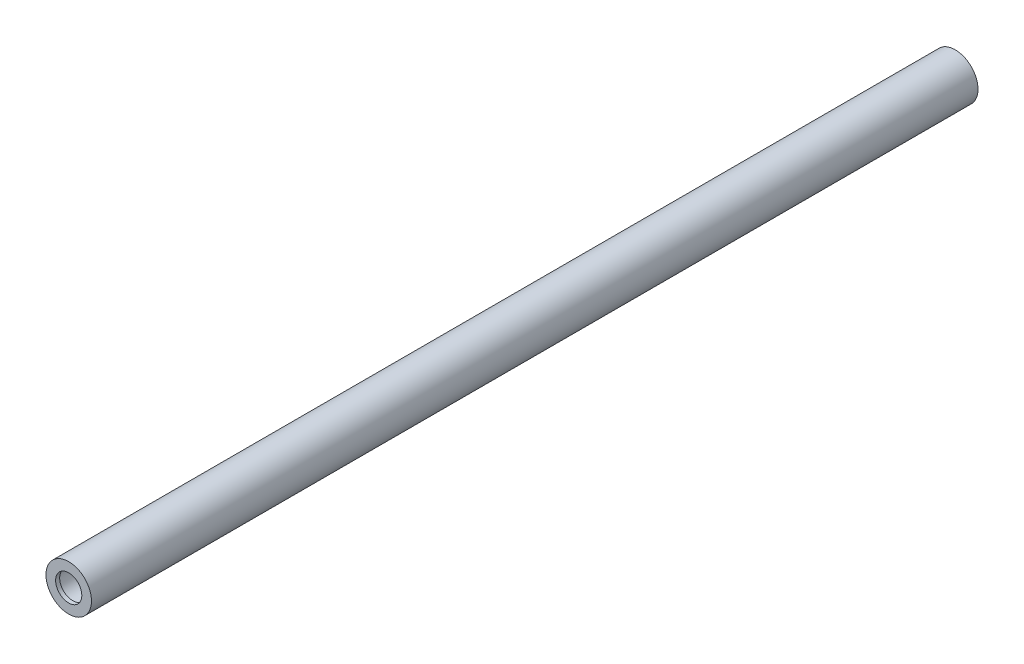
SolidWorks part; units mm, degrees
ref_plane "Front Plane" through (0, 0, 0) normal (0, 0, 1) x (1, 0, 0)
ref_plane "Top Plane" through (0, 0, 0) normal (0, 1, 0) x (1, 0, 0)
ref_plane "Right Plane" through (0, 0, 0) normal (1, 0, 0) x (0, 0, -1)
sketch "Sketch1" plane through (0, 0, 0) normal (0, 0, 1) x (1, 0, 0)
  circle A0 centre (0, 0) radius 11.295
  circle A1 centre (0, 0) radius 7.5
  dimension "D1" = 22.59
  dimension "D2" = 15
extrude "Boss-Extrude1" add sketch "Sketch1" along normal blind 440 contours A0 A1
ref_plane "Plane2" through (0, 0, 0) normal (0, 0, -1) x (-1, 0, 0)
sketch "Sketch4" plane through (0, 0, 0) normal (0, 0, -1) x (-1, 0, 0)
  circle A0 centre (0, 0) radius 6.5
  dimension "D1" = 13
extrude "Cut-Extrude4" cut sketch "Sketch4" against normal blind 2
ref_plane "Plane3" through (0, 0, 2) normal (0, 0, -1) x (-1, 0, 0)
sketch "Sketch5" plane through (0, 0, 2) normal (0, 0, -1) x (-1, 0, 0)
  circle A0 centre (0, 0) radius 7.5
  dimension "D1" = 15
extrude "Cut-Extrude5" cut sketch "Sketch5" against normal blind 15 contours A0
ref_plane "Plane4" through (0, 0, 440) normal (0, 0, 1) x (1, 0, 0)
sketch "Sketch6" plane through (0, 0, 440) normal (0, 0, 1) x (1, 0, 0)
  circle A0 centre (0, 0) radius 6.5
  dimension "D1" = 13
extrude "Cut-Extrude7" cut sketch "Sketch6" against normal blind 2 contours A0
ref_plane "Plane6" through (0, 0, 438) normal (0, 0, 1) x (1, 0, 0)
sketch "Sketch8" plane through (0, 0, 438) normal (0, 0, 1) x (1, 0, 0)
  circle A0 centre (0, 0) radius 7.5
  dimension "D1" = 15
extrude "Cut-Extrude8" cut sketch "Sketch8" against normal blind 15 contours A0
